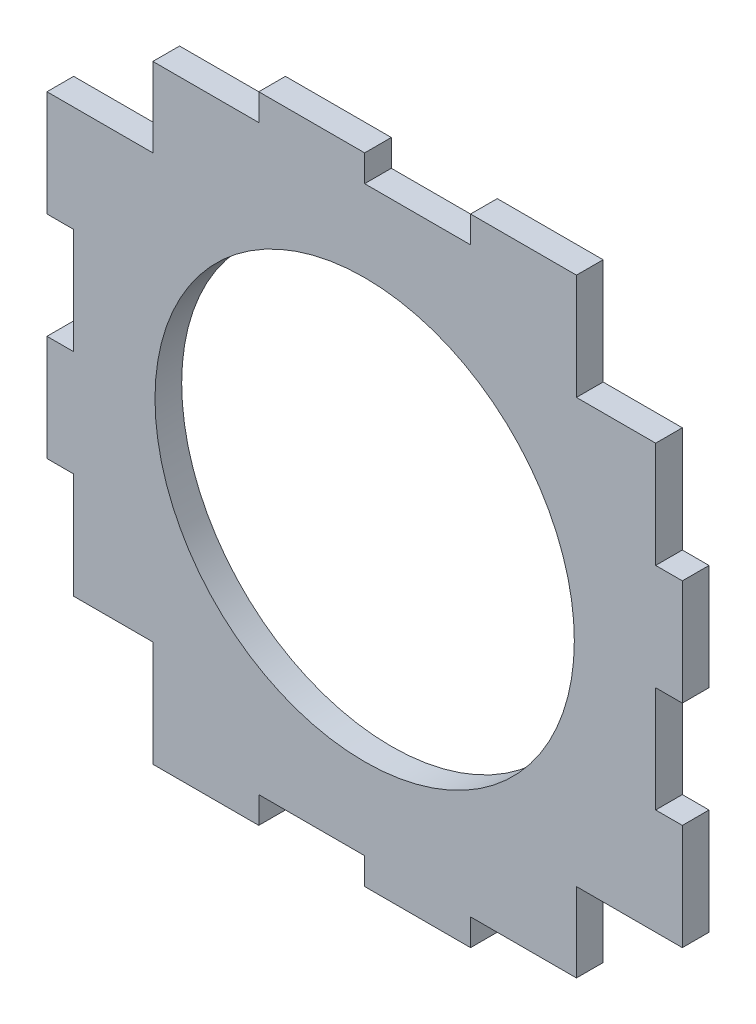
SolidWorks part; units mm, degrees
ref_plane "Front Plane" through (0, 0, 0) normal (0, 0, 1) x (1, 0, 0)
ref_plane "Top Plane" through (0, 0, 0) normal (0, 1, 0) x (1, 0, 0)
ref_plane "Right Plane" through (0, 0, 0) normal (1, 0, 0) x (0, 0, -1)
sketch "Sketch1" plane through (0, 0, 0) normal (0, 0, 1) x (1, 0, 0)
  line L0 (-21.6667, -30) -> (-21.6667, 20) construction
  line L1 (-30, -30) -> (20, -30) construction
  line L2 (-30, -30) -> (-30, 20) construction
  line L3 (-30, 20) -> (20, 20) construction
  line L4 (20, -30) -> (20, 20) construction
  line L5 (-30, -30) -> (20, 20) construction
  line L6 (-30, 20) -> (20, -30) construction
  line L7 (-13.3333, -30) -> (-13.3333, 20) construction
  line L8 (-5, -30) -> (-5, 20) construction
  line L9 (3.3333, -30) -> (3.3333, 20) construction
  line L10 (11.6667, -30) -> (11.6667, 20) construction
  line L11 (-30, -21.6667) -> (20, -21.6667) construction
  line L12 (-30, -13.3333) -> (20, -13.3333) construction
  line L13 (-30, -5) -> (20, -5) construction
  line L14 (-30, 3.3333) -> (20, 3.3333) construction
  line L15 (-30, 11.6667) -> (20, 11.6667) construction
  line L16 (-27.9, -30) -> (-27.9, 20) construction
  line L17 (17.9, -30) -> (17.9, 20) construction
  line L18 (20, -27.9) -> (-30, -27.9) construction
  line L19 (-30, 17.9) -> (20, 17.9) construction
  circle A0 centre (-5, -5) radius 19.25
  point P0 (-5, -5)
  dimension "D1" = 50
  dimension "D2" = 8.3333
  dimension "D3" = 8.3333
  dimension "D4" = 8.3333
  dimension "D5" = 8.3333
  dimension "D6" = 8.3333
  dimension "D7" = 8.3333
  dimension "D8" = 8.3333
  dimension "D9" = 8.3333
  dimension "D10" = 8.3333
  dimension "D11" = 8.3333
  dimension "D12" = 2.1
  dimension "D13" = 2.1
  dimension "D14" = 2.1
  dimension "D15" = 2.1
sketch "Sketch2" plane through (0, 0, 0) normal (0, 0, 1) x (1, 0, 0)
  line L0 (-30, 11.6667) -> (-21.6667, 11.6667)
  line L1 (-21.6667, -30) -> (-21.6667, 20) construction
  line L2 (-30, 11.6667) -> (20, 11.6667) construction
  line L3 (-21.6667, 11.6667) -> (-21.6667, 17.9)
  line L4 (-21.6667, 17.9) -> (-13.3333, 17.9)
  line L5 (-13.3333, -30) -> (-13.3333, 20) construction
  line L6 (-30, 17.9) -> (20, 17.9) construction
  line L7 (-13.3333, 17.9) -> (-13.3333, 20)
  line L8 (-13.3333, 20) -> (-5, 20)
  line L9 (-5, 20) -> (-5, 17.9)
  line L10 (-5, 17.9) -> (3.3333, 17.9)
  line L11 (3.3333, -30) -> (3.3333, 20) construction
  line L12 (3.3333, 17.9) -> (3.3333, 20)
  line L13 (3.3333, 20) -> (11.6667, 20)
  line L14 (11.6667, 20) -> (11.6667, 11.6667)
  line L15 (-30, -30) -> (20, 20) construction
  line L16 (11.6667, -30) -> (11.6667, 20) construction
  line L17 (11.6667, 11.6667) -> (17.9, 11.6667)
  line L18 (17.9, 11.6667) -> (17.9, 3.3333)
  line L19 (-30, 3.3333) -> (20, 3.3333) construction
  line L20 (17.9, -30) -> (17.9, 20) construction
  line L21 (17.9, 3.3333) -> (20, 3.3333)
  line L22 (20, 3.3333) -> (20, -5)
  line L23 (20, -5) -> (17.9, -5)
  line L24 (17.9, -5) -> (17.9, -13.3333)
  line L25 (-30, -13.3333) -> (20, -13.3333) construction
  line L26 (17.9, -13.3333) -> (20, -13.3333)
  line L27 (20, -13.3333) -> (20, -21.6667)
  line L28 (20, -21.6667) -> (11.6667, -21.6667)
  line L29 (-30, 20) -> (20, -30) construction
  line L30 (-30, -21.6667) -> (20, -21.6667) construction
  line L31 (11.6667, -21.6667) -> (11.6667, -27.9)
  line L32 (11.6667, -27.9) -> (3.3333, -27.9)
  line L33 (20, -27.9) -> (-30, -27.9) construction
  line L34 (3.3333, -27.9) -> (3.3333, -30)
  line L35 (3.3333, -30) -> (-5, -30)
  line L36 (-5, -30) -> (-5, -27.9)
  line L37 (-5, -27.9) -> (-13.3333, -27.9)
  line L38 (-13.3333, -27.9) -> (-13.3333, -30)
  line L39 (-13.3333, -30) -> (-21.6667, -30)
  line L40 (-21.6667, -30) -> (-21.6667, -21.6667)
  line L41 (-21.6667, -21.6667) -> (-27.9, -21.6667)
  line L42 (-27.9, -21.6667) -> (-27.9, -13.3333)
  line L43 (-27.9, -30) -> (-27.9, 20) construction
  line L44 (-27.9, -13.3333) -> (-30, -13.3333)
  line L45 (-30, -13.3333) -> (-30, -5)
  line L46 (-30, -30) -> (-30, 20) construction
  line L47 (-30, -5) -> (-27.9, -5)
  line L48 (-30, -5) -> (20, -5) construction
  line L49 (-27.9, -5) -> (-27.9, 3.3333)
  line L50 (-27.9, 3.3333) -> (-30, 3.3333)
  line L51 (-30, 3.3333) -> (-30, 11.6667)
  line L52 (-30, 20) -> (20, 20) construction
  line L53 (-5, -30) -> (-5, 20) construction
  line L54 (20, -30) -> (20, 20) construction
  circle A0 centre (-5, -5) radius 16.5
  dimension "D1" = 33
extrude "Boss-Extrude1" add sketch "Sketch2" along normal blind 2.1
equation "\"dim\"= 50"
equation "\"D1@Sketch1\"=\"dim\""
equation "\"thik\"= 2.1"
equation "\"D13@Sketch1\"=\"thik\""
equation "\"D14@Sketch1\"=\"thik\""
equation "\"D15@Sketch1\"=\"thik\""
equation "\"D12@Sketch1\"=\"thik\""
equation "\"D2@Sketch1\" = ( \"dim\" - \"dim\" * 4 / 6 ) / 2"
equation "\"D7@Sketch1\" = ( \"dim\" - \"dim\" * 4 / 6 ) / 2"
equation "\"D3@Sketch1\" = \"dim\" / 6"
equation "\"D4@Sketch1\" = \"dim\" / 6"
equation "\"D5@Sketch1\" = \"dim\" / 6"
equation "\"D6@Sketch1\" = \"dim\" / 6"
equation "\"D8@Sketch1\"=\"dim\"/6"
equation "\"D9@Sketch1\" = \"dim\" / 6"
equation "\"D10@Sketch1\" = \"dim\" / 6"
equation "\"D11@Sketch1\" = \"dim\" / 6"
equation "\"D1@Boss-Extrude1\"=\"thik\""
